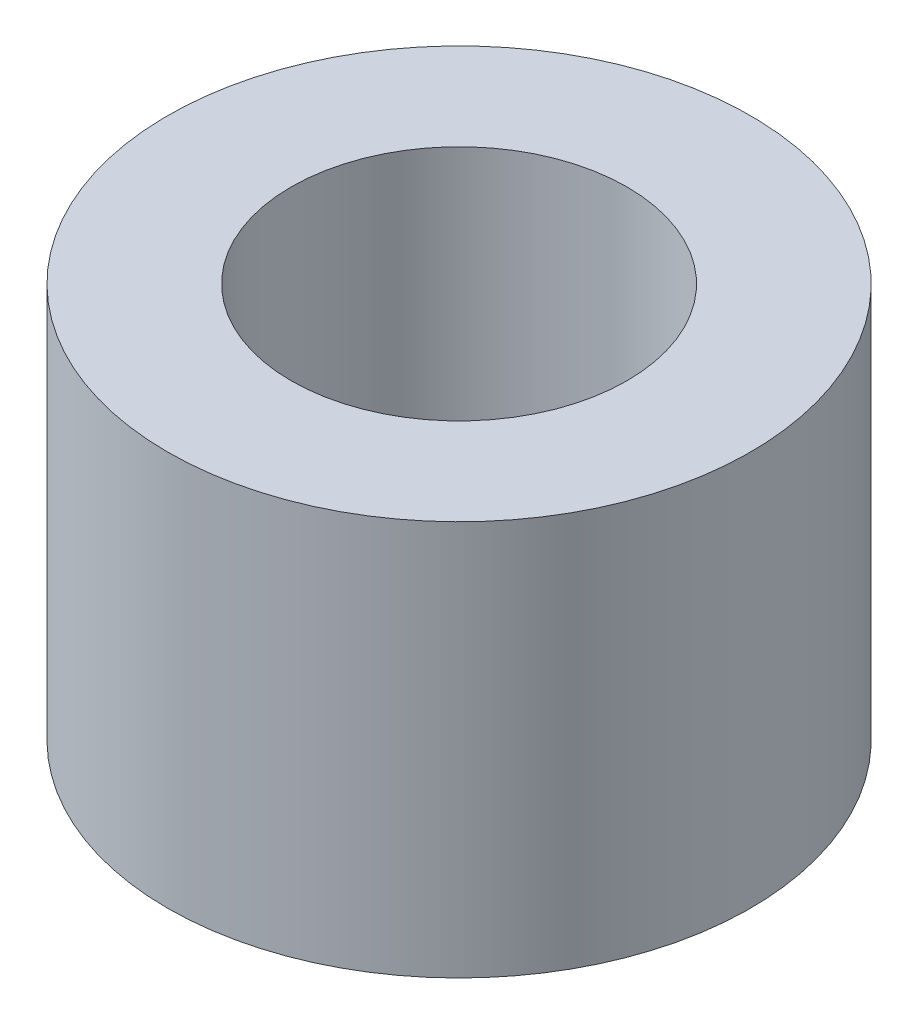
SolidWorks part; units mm, degrees
ref_plane "Front Plane" through (0, 0, 0) normal (0, 0, 1) x (1, 0, 0)
ref_plane "Top Plane" through (0, 0, 0) normal (0, 1, 0) x (1, 0, 0)
ref_plane "Right Plane" through (0, 0, 0) normal (1, 0, 0) x (0, 0, -1)
sketch "Sketch2" plane through (0, 0, 0) normal (0, 1, 0) x (1, 0, 0)
  circle A0 centre (0, 0) radius 1.7
  circle A1 centre (0, 0) radius 2.95
  dimension "D1" = 3.4
  dimension "D2" = 1.25
extrude "Boss-Extrude1" add sketch "Sketch2" along normal blind 4
